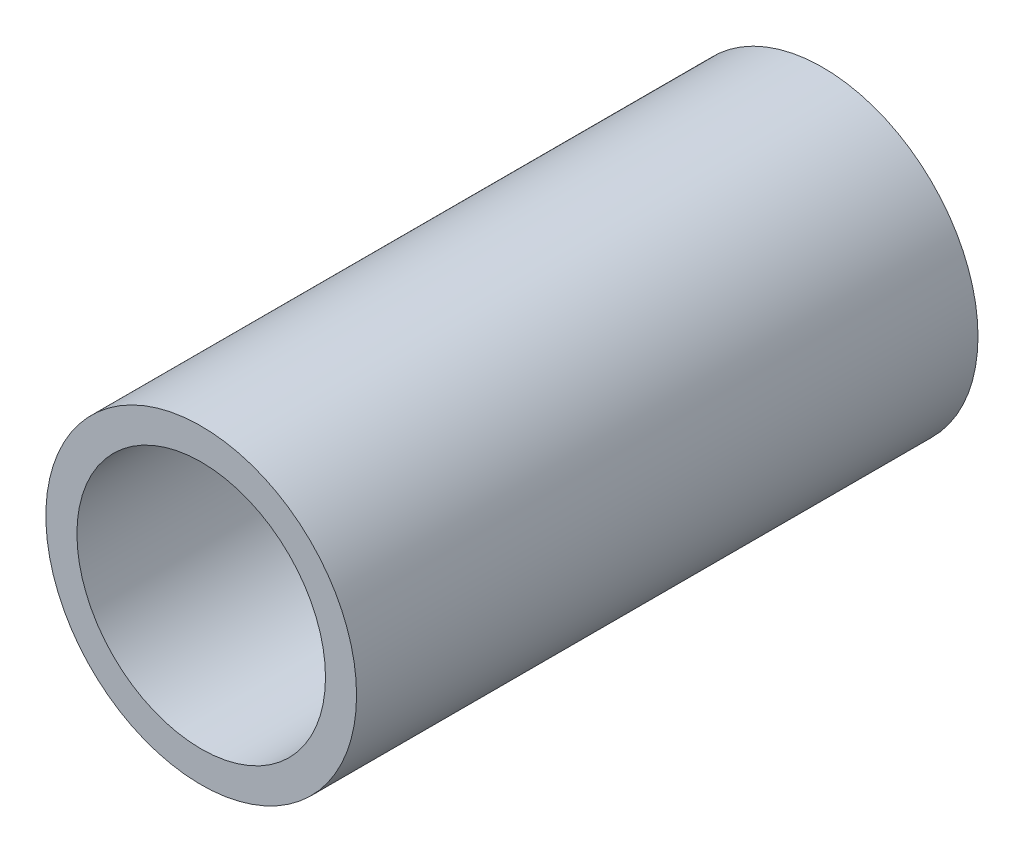
SolidWorks part; units mm, degrees
ref_plane "Front Plane" through (0, 0, 0) normal (0, 0, 1) x (1, 0, 0)
ref_plane "Top Plane" through (0, 0, 0) normal (0, 1, 0) x (1, 0, 0)
ref_plane "Right Plane" through (0, 0, 0) normal (1, 0, 0) x (0, 0, -1)
sketch "Sketch1" plane through (0, 0, 0) normal (0, 0, 1) x (1, 0, 0)
  circle A0 centre (0, 0) radius 40
  circle A1 centre (0, 0) radius 50
  dimension "D1" = 100
  dimension "D2" = 10
extrude "Extrude1" add sketch "Sketch1" along normal blind 200
